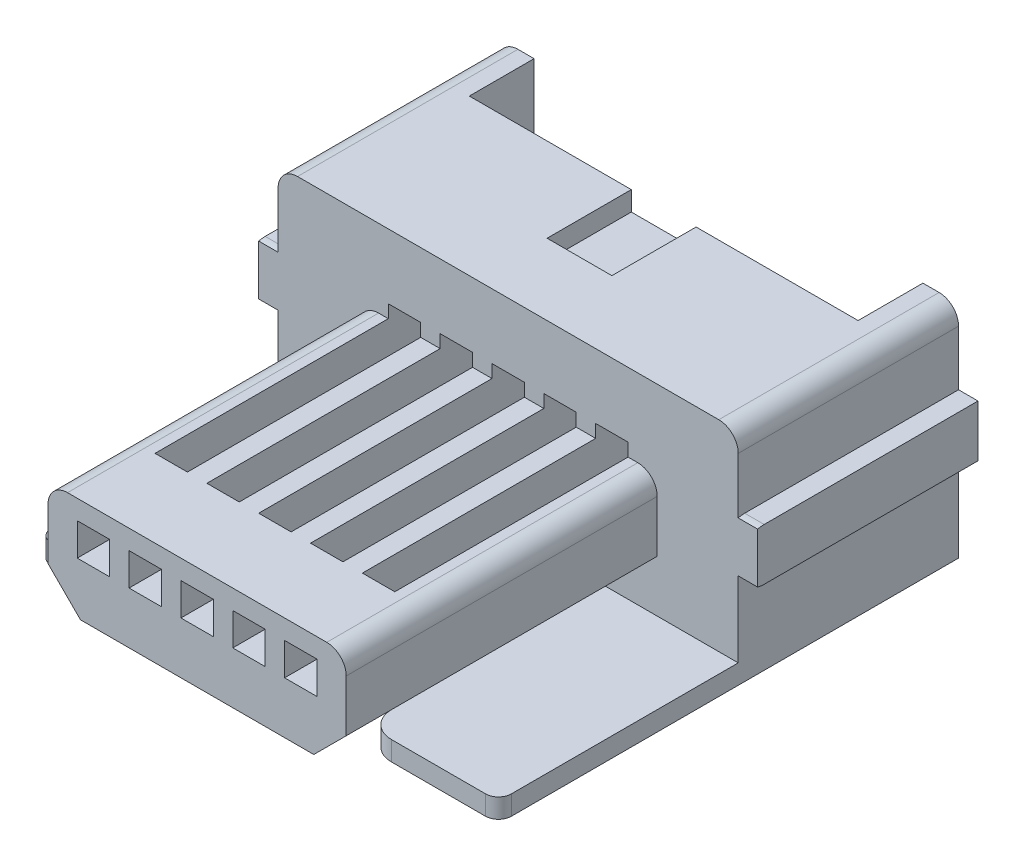
SolidWorks part; units mm, degrees
material "普通碳钢"
ref_plane "Front Plane" through (0, 0, 0) normal (0, 0, 1) x (1, 0, 0)
ref_plane "Top Plane" through (0, 0, 0) normal (0, 1, 0) x (1, 0, 0)
ref_plane "Right Plane" through (0, 0, 0) normal (1, 0, 0) x (0, 0, -1)
sketch "Sketch1" plane through (0, 0, 0) normal (0, 0, 1) x (1, 0, 0)
  line L0 (55, 0) -> (-55, 0) construction
  line L1 (-3.25, 3.4) -> (3.25, 3.4)
  line L2 (-3.55, 3.1) -> (-3.55, 0)
  line L3 (-3.55, 0) -> (3.55, 0)
  line L4 (3.55, 3.1) -> (3.55, 0)
  arc A0 (-3.55, 3.1) -> (-3.25, 3.4) centre (-3.25, 3.1) cw
  arc A1 (3.55, 3.1) -> (3.25, 3.4) centre (3.25, 3.1) ccw
  point P9 (-3.55, 3.4)
  point P12 (3.55, 3.4)
  dimension "D3" = 0.3
  dimension "D1" = 3.4
  dimension "D2" = 7.1
extrude "Boss-Extrude1" add sketch "Sketch1" along normal blind 8.2
sketch "Sketch2" plane through (0, 0, 0) normal (1, 0, 0) x (0, 0, -1)
  line L0 (0, 2.25) -> (-3.3, 2.25)
  line L1 (0, 1.87) -> (0, -1.87) construction
  line L2 (3.905, 0) -> (-3.905, 0) construction
  line L3 (0, 1.45) -> (-3.3, 1.45)
  line L4 (0, 2.25) -> (0, 1.45)
  arc A0 (-3.3, 2.25) -> (-3.3, 1.45) centre (-3.3, 1.85) ccw
  dimension "D1" = 0.8
  dimension "D2" = 1.45
  dimension "D3" = 3.3
extrude "Boss-Extrude2" add sketch "Sketch2" along normal mid plane 7.7
sketch "Sketch3" plane through (0, 0, 8.2) normal (0, 0, 1) x (1, 0, 0)
  line L0 (4.235, 0) -> (-4.235, 0) construction
  line L1 (-2, 2.2) -> (2, 2.2)
  line L2 (-2.3, 1.9) -> (-2.3, 1.1)
  line L3 (-1.8, 0.6) -> (1.8, 0.6)
  line L4 (2.3, 1.9) -> (2.3, 1.1)
  line L5 (0, -1.87) -> (0, 1.87) construction
  line L6 (-2.3, 1.1) -> (-1.8, 0.6)
  line L7 (1.8, 0.6) -> (2.3, 1.1)
  arc A0 (2, 2.2) -> (2.3, 1.9) centre (2, 1.9) cw
  arc A1 (-2, 2.2) -> (-2.3, 1.9) centre (-2, 1.9) ccw
  point P1 (2.3, 0.6)
  point P2 (-2.3, 0.6)
  point P14 (2.3, 2.2)
  dimension "D5" = 0.3
  dimension "D1" = 4.6
  dimension "D2" = 1.6
  dimension "D3" = 0.6
  dimension "D4" = 2.3
extrude "Cut-Extrude1" cut sketch "Sketch3" against normal blind 4.8 flip side to cut
sketch "Sketch4" plane through (0, 0, 0) normal (0, 0, 1) x (1, 0, 0)
  line L0 (3.25, 3.4) -> (-3.25, 3.4) construction
  line L1 (0.5, 3.4) -> (-0.5, 3.4)
  line L2 (0.5, 3.4) -> (0.5, 3.1)
  line L3 (0.5, 3.1) -> (-0.5, 3.1)
  line L4 (-0.5, 3.4) -> (-0.5, 3.1)
  line L5 (0, -1.87) -> (0, 1.87) construction
  dimension "D1" = 1
  dimension "D2" = 0.5
  dimension "D3" = 0.3
extrude "Cut-Extrude3" cut sketch "Sketch4" along normal blind 2.3
sketch "Sketch5" plane through (0, 0, 0) normal (0, 1, 0) x (1, 0, 0)
  line L0 (-1.87, 0) -> (1.87, 0) construction
  line L1 (-1.85, 0) -> (1.85, 0)
  line L2 (-1.85, 0) -> (-1.85, -1)
  line L3 (-1.85, -1) -> (-1.35, -1)
  line L4 (1.85, 0) -> (1.85, -1)
  line L5 (0, -1.87) -> (0, 1.87) construction
  line L6 (-1.05, -1) -> (-0.55, -1)
  line L7 (-1.35, -0.7) -> (-1.05, -0.7)
  line L8 (-1.35, -0.7) -> (-1.35, -1)
  line L9 (-0.25, -1) -> (0.25, -1)
  line L10 (-1.05, -0.7) -> (-1.05, -1)
  line L11 (-0.55, -0.7) -> (-0.25, -0.7)
  line L12 (-0.55, -0.7) -> (-0.55, -1)
  line L13 (0.55, -1) -> (1.05, -1)
  line L14 (-0.25, -0.7) -> (-0.25, -1)
  line L15 (0.25, -0.7) -> (0.55, -0.7)
  line L16 (0.25, -0.7) -> (0.25, -1)
  line L17 (1.35, -1) -> (1.85, -1)
  line L18 (0.55, -0.7) -> (0.55, -1)
  line L19 (1.05, -0.7) -> (1.35, -0.7)
  line L20 (1.05, -0.7) -> (1.05, -1)
  line L22 (1.35, -0.7) -> (1.35, -1)
  dimension "D1" = 3.7
  dimension "D2" = 1.85
  dimension "D3" = 0.3
  dimension "D4" = 0.5
  dimension "D5" = 1
extrude "Cut-Extrude6" cut sketch "Sketch5" along normal through all
sketch "Sketch6" plane through (0, 0, 8.2) normal (0, 0, 1) x (1, 0, 0)
  line L0 (1.85, 3.4) -> (1.85, 0) construction
  line L1 (1.85, 1.9) -> (1.35, 1.9)
  line L2 (1.85, 1.9) -> (1.85, 1.4)
  line L3 (1.85, 1.4) -> (1.35, 1.4)
  line L4 (1.35, 1.9) -> (1.35, 1.4)
  line L5 (1.35, 3.4) -> (1.35, 0) construction
  line L6 (1.05, 3.4) -> (1.05, 0) construction
  line L7 (1.05, 1.9) -> (0.55, 1.9)
  line L8 (1.05, 1.9) -> (1.05, 1.4)
  line L9 (1.05, 1.4) -> (0.55, 1.4)
  line L10 (0.55, 1.9) -> (0.55, 1.4)
  line L11 (0.55, 3.4) -> (0.55, 0) construction
  line L12 (0.25, 3.1) -> (0.25, 0) construction
  line L13 (0.25, 1.9) -> (-0.25, 1.9)
  line L14 (0.25, 1.9) -> (0.25, 1.4)
  line L15 (0.25, 1.4) -> (-0.25, 1.4)
  line L16 (-0.25, 1.9) -> (-0.25, 1.4)
  line L17 (-0.25, 3.1) -> (-0.25, 0) construction
  line L18 (-0.55, 3.4) -> (-0.55, 0) construction
  line L19 (-0.55, 1.9) -> (-1.05, 1.9)
  line L20 (-0.55, 1.9) -> (-0.55, 1.4)
  line L21 (-0.55, 1.4) -> (-1.05, 1.4)
  line L22 (-1.05, 1.9) -> (-1.05, 1.4)
  line L23 (-1.05, 3.4) -> (-1.05, 0) construction
  line L24 (-1.35, 3.4) -> (-1.35, 0) construction
  line L25 (-1.35, 1.9) -> (-1.85, 1.9)
  line L26 (-1.35, 1.9) -> (-1.35, 1.4)
  line L27 (-1.35, 1.4) -> (-1.85, 1.4)
  line L28 (-1.85, 1.9) -> (-1.85, 1.4)
  line L29 (-1.85, 3.4) -> (-1.85, 0) construction
  line L30 (4.235, 0) -> (-4.235, 0) construction
  dimension "D1" = 1.9
  dimension "D2" = 0.5
extrude "Cut-Extrude7" cut sketch "Sketch6" against normal blind 2
sketch "Sketch7" plane through (0, 0, 0) normal (0, 0, 1) x (1, 0, 0)
  line L0 (1.85, 3.4) -> (1.85, 0) construction
  line L1 (1.85, 2.4) -> (1.35, 2.4)
  line L2 (1.85, 2.4) -> (1.85, 1.6)
  line L3 (1.85, 1.6) -> (1.35, 1.6)
  line L4 (1.35, 2.4) -> (1.35, 1.6)
  line L5 (1.05, 3.4) -> (1.05, 0) construction
  line L6 (1.05, 2.4) -> (0.55, 2.4)
  line L7 (1.05, 2.4) -> (1.05, 1.6)
  line L8 (1.05, 1.6) -> (0.55, 1.6)
  line L9 (0.55, 2.4) -> (0.55, 1.6)
  line L10 (0.25, 3.1) -> (0.25, 0) construction
  line L11 (0.25, 2.4) -> (-0.25, 2.4)
  line L12 (0.25, 2.4) -> (0.25, 1.6)
  line L13 (0.25, 1.6) -> (-0.25, 1.6)
  line L14 (-0.25, 2.4) -> (-0.25, 1.6)
  line L16 (-0.55, 3.4) -> (-0.55, 0) construction
  line L17 (-0.55, 2.4) -> (-1.05, 2.4)
  line L18 (-0.55, 2.4) -> (-0.55, 1.6)
  line L19 (-0.55, 1.6) -> (-1.05, 1.6)
  line L20 (-1.05, 2.4) -> (-1.05, 1.6)
  line L21 (-1.85, 3.4) -> (-1.85, 0) construction
  line L22 (-1.35, 1.6) -> (-1.85, 1.6)
  line L23 (-1.35, 1.6) -> (-1.35, 2.4)
  line L24 (-1.35, 2.4) -> (-1.85, 2.4)
  line L25 (-1.85, 1.6) -> (-1.85, 2.4)
  line L26 (-1.05, 3.4) -> (-1.05, 0) construction
  line L29 (4.235, 0) -> (-4.235, 0) construction
  line L30 (-0.25, 1.9) -> (-0.25, 1.4) construction
  line L31 (-1.35, 1.4) -> (-1.35, 1.9) construction
  line L32 (1.35, 1.9) -> (1.35, 1.4) construction
  line L33 (0.55, 1.9) -> (0.55, 1.4) construction
  dimension "D1" = 0.8
  dimension "D2" = 1.6
extrude "Cut-Extrude8" cut sketch "Sketch7" along normal blind 7
sketch "Sketch8" plane through (0, 3.4, 0) normal (0, 1, 0) x (1, 0, 0)
  line L0 (-1.87, 0) -> (1.87, 0) construction
  line L1 (-3, 0) -> (3, 0)
  line L2 (-3, 0) -> (-3, -1)
  line L3 (-3, -1) -> (3, -1)
  line L4 (3, 0) -> (3, -1)
  line L5 (1.35, -1) -> (1.85, -1) construction
  line L6 (0, -1.87) -> (0, 1.87) construction
  dimension "D1" = 6
  dimension "D2" = 3
extrude "Cut-Extrude9" cut sketch "Sketch8" against normal blind 2
sketch "Sketch9" plane through (0, 0, 0) normal (0, 0, 1) x (1, 0, 0)
  line L0 (4.235, 0) -> (-4.235, 0) construction
  line L1 (3, 0.5) -> (-3, 0.5)
  line L2 (3, 0.5) -> (3, 0)
  line L3 (3, 0) -> (-3, 0)
  line L4 (-3, 0.5) -> (-3, 0)
  line L5 (-3, 1.4) -> (-3, 3.4) construction
  line L6 (3, 1.4) -> (3, 3.4) construction
  dimension "D1" = 0.5
extrude "Cut-Extrude10" cut sketch "Sketch9" along normal blind 1
sketch "Sketch10" plane through (0, 0, 0) normal (0, -1, 0) x (1, 0, 0)
  line L0 (-3.55, 3.4) -> (3.55, 3.4) construction
  line L1 (0, -2.475) -> (0, 2.475) construction
  circle A0 centre (2.2, 3.05) radius 0.4
  circle A1 centre (-2.2, 3.05) radius 0.4
  dimension "D1" = 0.8
  dimension "D2" = 0.35
  dimension "D3" = 2.2
  dimension "D4" = 4.4
extrude "Boss-Extrude3" add sketch "Sketch10" along normal blind 1.1
chamfer "Chamfer1" distance 0.2 angle 45 2 edges at (2.2, -1.1, 2.65) (-2.2, -1.1, 2.65)
sketch "Sketch11" plane through (0, 0, 3.4) normal (0, 0, 1) x (1, 0, 0)
  line L0 (-3.55, 1.4627) -> (-3.55, 0) construction
  line L1 (-3.55, 0.3) -> (3.55, 0.3)
  line L2 (-3.55, 0.3) -> (-3.55, 0)
  line L3 (-3.55, 0) -> (3.55, 0)
  line L4 (3.55, 0.3) -> (3.55, 0)
  line L5 (4.235, 0) -> (-4.235, 0) construction
  line L6 (3.55, 0) -> (3.55, 1.4627) construction
  dimension "D1" = 0.3
extrude "Boss-Extrude4" add sketch "Sketch11" along normal blind 3.7
fillet "Fillet1" radius 0.2 2 edges at (3.55, 0.15, 7.1) (-3.55, 0.15, 7.1)
sketch "Sketch12" plane through (0, 0, 0) normal (0, -1, 0) x (1, 0, 0)
  line L0 (-3.35, 7.1) -> (3.35, 7.1) construction
  line L1 (-1.5, 7.1) -> (1.5, 7.1)
  line L2 (-1.5, 7.1) -> (-1.5, 5.1)
  line L3 (-1.5, 5.1) -> (1.5, 5.1)
  line L4 (1.5, 7.1) -> (1.5, 5.1)
  line L5 (0, -2.475) -> (0, 2.475) construction
  dimension "D1" = 3
  dimension "D2" = 1.5
  dimension "D3" = 2
extrude "Cut-Extrude11" cut sketch "Sketch12" against normal blind 0.5
fillet "Fillet2" radius 0.2 2 edges at (-1.5, 0.15, 5.1) (1.5, 0.15, 5.1)
fillet "Fillet3" radius 0.4 2 edges at (-1.5, 0.15, 7.1) (1.5, 0.15, 7.1)
